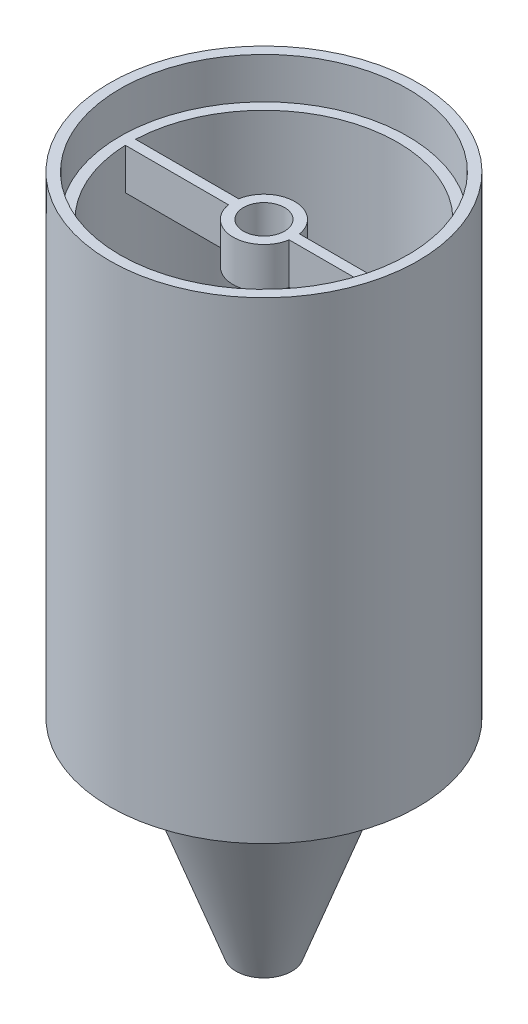
SolidWorks part; units mm, degrees
ref_plane "Front Plane" through (0, 0, 0) normal (0, 0, 1) x (1, 0, 0)
ref_plane "Top Plane" through (0, 0, 0) normal (0, 1, 0) x (1, 0, 0)
ref_plane "Right Plane" through (0, 0, 0) normal (1, 0, 0) x (0, 0, -1)
sketch "Sketch1" plane through (0, 0, 0) normal (0, 1, 0) x (1, 0, 0)
  circle A0 centre (0, 0) radius 19.05
  dimension "D1" = 38.1
extrude "Boss-Extrude1" add sketch "Sketch1" along normal blind 2.54
sketch "Sketch2" plane through (0, 0, 0) normal (0, -1, 0) x (1, 0, 0)
  circle A0 centre (0, 0) radius 12.7
  dimension "D1" = 25.4
extrude "Boss-Extrude2" add sketch "Sketch2" along normal blind 25.4 draft 20
sketch "Sketch3" plane through (0, -25.4, 0) normal (0, -1, 0) x (1, 0, 0)
  circle A0 centre (0, 0) radius 2.54
  dimension "D1" = 5.08
extrude "Cut-Extrude1" cut sketch "Sketch3" against normal up to next (27.94 mm away) draft 20 draft outward yes
sketch "Sketch4" plane through (0, 2.54, 0) normal (0, 1, 0) x (1, 0, 0)
  circle A0 centre (0, 0) radius 19.05
  circle A1 centre (0, 0) radius 16.51
  circle A2 centre (0, 0) radius 19.05 construction
  dimension "D1" = 2.54
extrude "Boss-Extrude3" add sketch "Sketch4" along normal blind 50.8
sketch "Sketch5" plane through (0, 53.34, 0) normal (0, 1, 0) x (1, 0, 0)
  line L0 (3.7567, 0.635) -> (16.4978, 0.635)
  line L1 (0, 0) -> (0, -19.05) construction
  line L2 (3.7567, -0.635) -> (16.4978, -0.635)
  line L3 (-3.7567, -0.635) -> (-16.4978, -0.635)
  line L4 (-3.7567, 0.635) -> (-16.4978, 0.635)
  circle A0 centre (0, 0) radius 2.54
  circle A1 centre (0, 0) radius 3.81 construction
  circle A2 centre (0, 0) radius 2.54 construction
  circle A3 centre (0, 0) radius 19.05
  circle A4 centre (0, 0) radius 16.51 construction
  circle A5 centre (0, 0) radius 19.05 construction
  circle A6 centre (0, 0) radius 16.51 construction
  arc A7 (-16.4978, -0.635) -> (16.4978, -0.635) centre (0, 0) ccw
  arc A8 (16.4978, 0.635) -> (-16.4978, 0.635) centre (0, 0) ccw
  arc A9 (-3.7567, 0.635) -> (3.7567, 0.635) centre (0, 0) cw
  arc A10 (-3.7567, -0.635) -> (3.7567, -0.635) centre (0, 0) ccw
  dimension "D1" = 1.27
  dimension "D2" = 1.27
extrude "Boss-Extrude4" add sketch "Sketch5" against normal blind 5.08
sketch "Sketch6" plane through (0, 53.34, 0) normal (0, 1, 0) x (1, 0, 0)
  circle A0 centre (0, 0) radius 19.05
  circle A1 centre (0, 0) radius 17.78
  circle A2 centre (0, 0) radius 19.05 construction
  dimension "D1" = 1.27
extrude "Boss-Extrude5" add sketch "Sketch6" along normal blind 5.08
